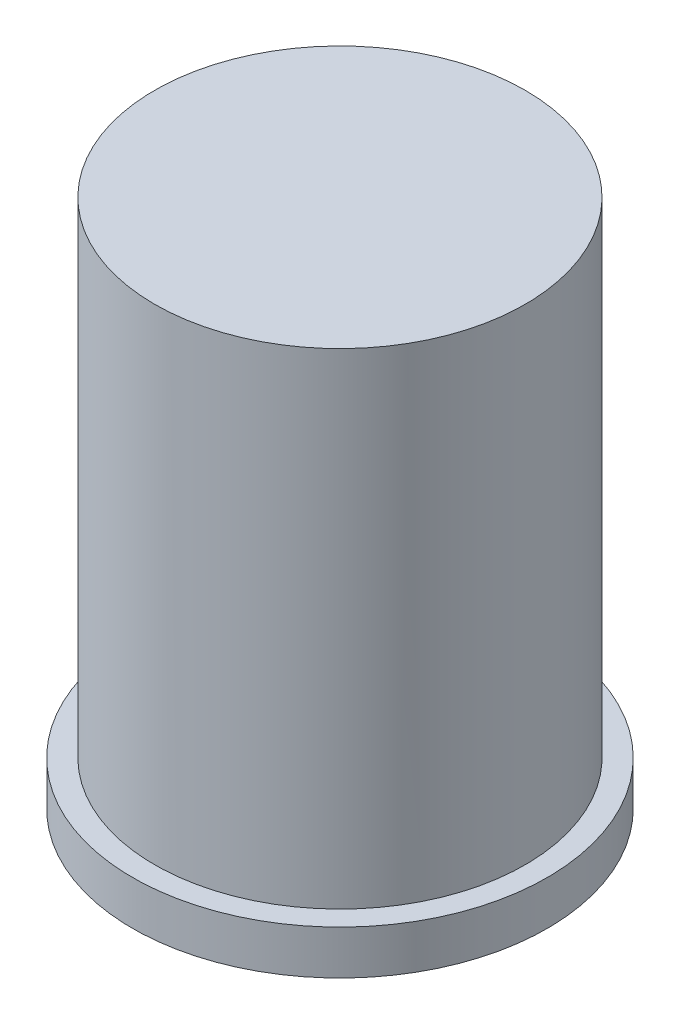
SolidWorks part; units mm, degrees
ref_plane "Front Plane" through (0, 0, 0) normal (0, 0, 1) x (1, 0, 0)
ref_plane "Top Plane" through (0, 0, 0) normal (0, 1, 0) x (1, 0, 0)
ref_plane "Right Plane" through (0, 0, 0) normal (1, 0, 0) x (0, 0, -1)
sketch "Sketch1" plane through (0, 0, 0) normal (0, 1, 0) x (1, 0, 0)
  circle A0 centre (0, 0) radius 42
  dimension "D1" = 84
extrude "Boss-Extrude1" add sketch "Sketch1" along normal blind 120
sketch "Sketch2" plane through (0, 0, 0) normal (0, -1, 0) x (1, 0, 0)
  circle A2 centre (0, 0) radius 47
  circle A3 centre (0, 0) radius 47
  circle A5 centre (0, 0) radius 42
  circle A6 centre (0, 0) radius 42
  dimension "D1" = 5
  dimension "D2" = 0
extrude "Boss-Extrude2" add sketch "Sketch2" against normal blind 10
